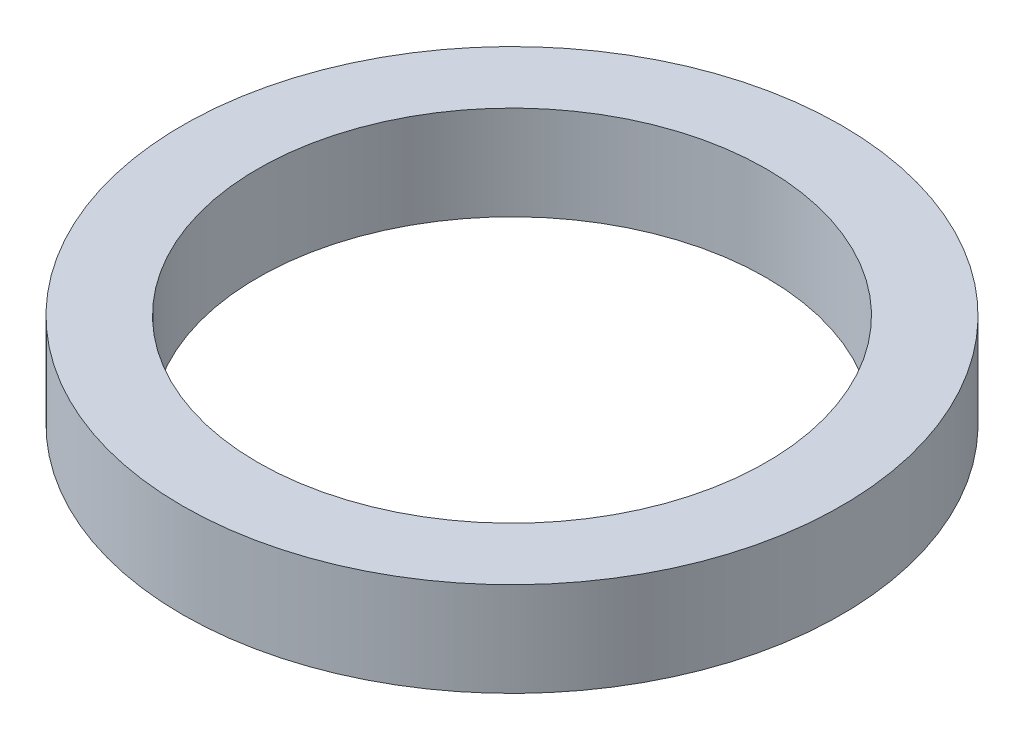
SolidWorks part; units mm, degrees
ref_plane "Front Plane" through (0, 0, 0) normal (0, 0, 1) x (1, 0, 0)
ref_plane "Top Plane" through (0, 0, 0) normal (0, 1, 0) x (1, 0, 0)
ref_plane "Right Plane" through (0, 0, 0) normal (1, 0, 0) x (0, 0, -1)
sketch "Sketch2" plane through (0, 0, 0) normal (0, 1, 0) x (1, 0, 0)
  circle A0 centre (0, 0) radius 3.5
  circle A1 centre (0, 0) radius 2.7
  dimension "D1" = 5.4
  dimension "D2" = 7
extrude "Boss-Extrude1" add sketch "Sketch2" along normal blind 1
